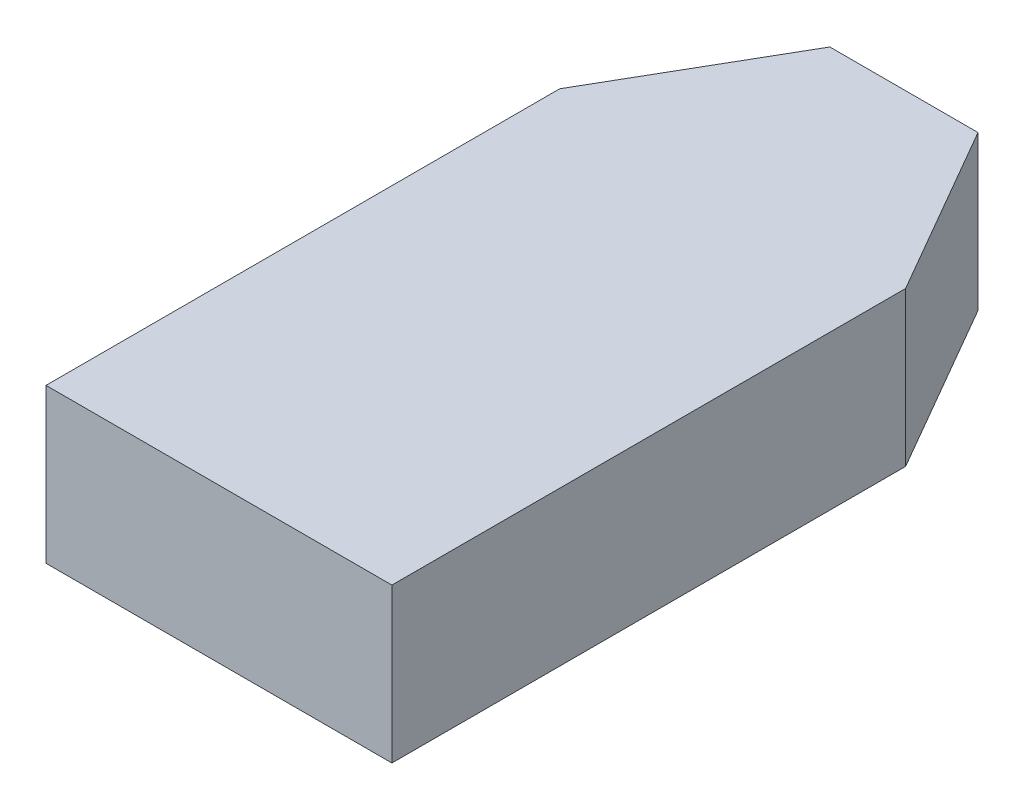
SolidWorks part; units mm, degrees
ref_plane "Спереди" through (0, 0, 0) normal (0, 0, 1) x (1, 0, 0)
ref_plane "Сверху" through (0, 0, 0) normal (0, 1, 0) x (1, 0, 0)
ref_plane "Справа" through (0, 0, 0) normal (1, 0, 0) x (0, 0, -1)
sketch "Эскиз1" plane through (0, 0, 0) normal (0, 1, 0) x (1, 0, 0)
  line L0 (0, 30) -> (0, 0)
  line L1 (5.7735, 40) -> (14.4265, 40)
  line L2 (0, 30) -> (5.7735, 40)
  line L3 (0, 0) -> (20.2, 0)
  line L4 (20.2, 30) -> (14.4265, 40)
  line L5 (0, 30) -> (20.2, 30) construction
  line L6 (0, 27.0295) -> (0, 40.5074) construction
  line L7 (20.2, 30) -> (20.2, 0)
  line L8 (20.2, 27.6713) -> (20.2, 40.5074) construction
  point P0 (0, 0)
  dimension "D1" = 30
  dimension "D2" = 30
  dimension "D3" = 30
  dimension "D4" = 40
  dimension "D5" = 20.2
extrude "Бобышка-Вытянуть1" add sketch "Эскиз1" along normal blind 9
